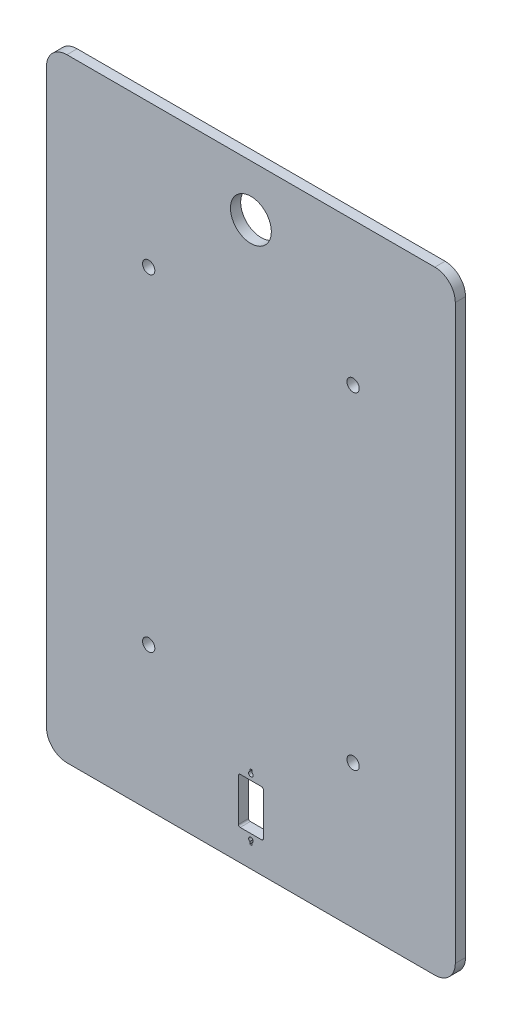
SolidWorks part; units mm, degrees
material "Maple"
ref_plane "Front Plane" through (0, 0, 0) normal (0, 0, 1) x (1, 0, 0)
ref_plane "Top Plane" through (0, 0, 0) normal (0, 1, 0) x (1, 0, 0)
ref_plane "Right Plane" through (0, 0, 0) normal (1, 0, 0) x (0, 0, -1)
sketch "Sketch1" plane through (0, 0, 0) normal (0, 0, 1) x (1, 0, 0)
  line L0 (0, 150) -> (0, -150) construction
  line L1 (-90, 150) -> (90, 150)
  line L2 (-100, 140) -> (-100, -140)
  line L3 (-90, -150) -> (90, -150)
  line L4 (100, 140) -> (100, -140)
  line L5 (-100, 0) -> (100, 0) construction
  line L9 (-0.55, -138.6026) -> (-0.55, -139.8)
  line L10 (0.55, -139.8) -> (0.55, -138.6026)
  line L11 (-0.55, -139.8) -> (0.55, -139.8)
  line L12 (-0.55, -138.6026) -> (-0.55, -139.8)
  line L13 (0.55, -139.8) -> (0.55, -138.6026)
  line L14 (-0.55, -139.8) -> (0.55, -139.8)
  line L15 (-0.55, -107.7) -> (-0.55, -108.8974)
  line L16 (0.55, -108.8974) -> (0.55, -107.7)
  line L17 (0.55, -107.7) -> (-0.55, -107.7)
  line L18 (-0.55, -107.7) -> (-0.55, -108.8974)
  line L19 (0.55, -108.8974) -> (0.55, -107.7)
  line L20 (0.55, -107.7) -> (-0.55, -107.7)
  line L22 (-6.1, -113.35) -> (-6.1, -134.15)
  line L23 (5.25, -112.5) -> (-5.25, -112.5)
  line L24 (6.1, -134.15) -> (6.1, -113.35)
  line L25 (-5.25, -135) -> (5.25, -135)
  line L26 (-6.1, -113.35) -> (-6.1, -134.15)
  line L27 (5.25, -112.5) -> (-5.25, -112.5)
  line L28 (6.1, -134.15) -> (6.1, -113.35)
  line L29 (-5.25, -135) -> (5.25, -135)
  circle A0 centre (0, 125) radius 10
  circle A1 centre (50, 80) radius 3
  circle A2 centre (-50, 80) radius 3
  circle A3 centre (-50, -80) radius 3
  circle A4 centre (50, -80) radius 3
  arc A5 (-100, -140) -> (-90, -150) centre (-90, -140) ccw
  arc A6 (90, -150) -> (100, -140) centre (90, -140) ccw
  arc A7 (-90, 150) -> (-100, 140) centre (-90, 140) ccw
  arc A8 (90, 150) -> (100, 140) centre (90, 140) cw
  arc A17 (0.55, -138.6026) -> (-0.55, -138.6026) centre (0, -137.65) ccw
  arc A18 (0.55, -138.6026) -> (-0.55, -138.6026) centre (0, -137.65) ccw
  arc A19 (-0.55, -108.8974) -> (0.55, -108.8974) centre (0, -109.85) ccw
  arc A20 (-0.55, -108.8974) -> (0.55, -108.8974) centre (0, -109.85) ccw
  arc A50 (-5.25, -112.5) -> (-6.1, -113.35) centre (-5.25, -113.35) ccw
  arc A51 (-5.25, -112.5) -> (-6.1, -113.35) centre (-5.25, -113.35) ccw
  arc A52 (6.1, -113.35) -> (5.25, -112.5) centre (5.25, -113.35) ccw
  arc A53 (6.1, -113.35) -> (5.25, -112.5) centre (5.25, -113.35) ccw
  arc A54 (5.25, -135) -> (6.1, -134.15) centre (5.25, -134.15) ccw
  arc A55 (5.25, -135) -> (6.1, -134.15) centre (5.25, -134.15) ccw
  arc A56 (-6.1, -134.15) -> (-5.25, -135) centre (-5.25, -134.15) ccw
  arc A57 (-6.1, -134.15) -> (-5.25, -135) centre (-5.25, -134.15) ccw
  point P8 (0, 0)
  point P25 (100, -150)
  point P28 (-100, 150)
  point P31 (100, 150)
  dimension "D3" = 20
  dimension "D4" = 25
  dimension "D5" = 6
  dimension "D6" = 50
  dimension "D7" = 80
  dimension "D8" = 10
  dimension "D1" = 200
  dimension "D2" = 300
  dimension "D9" = 0
  dimension "D10" = 0
  dimension "D11" = 0
extrude "Boss-Extrude1" add sketch "Sketch1" along normal blind 5
